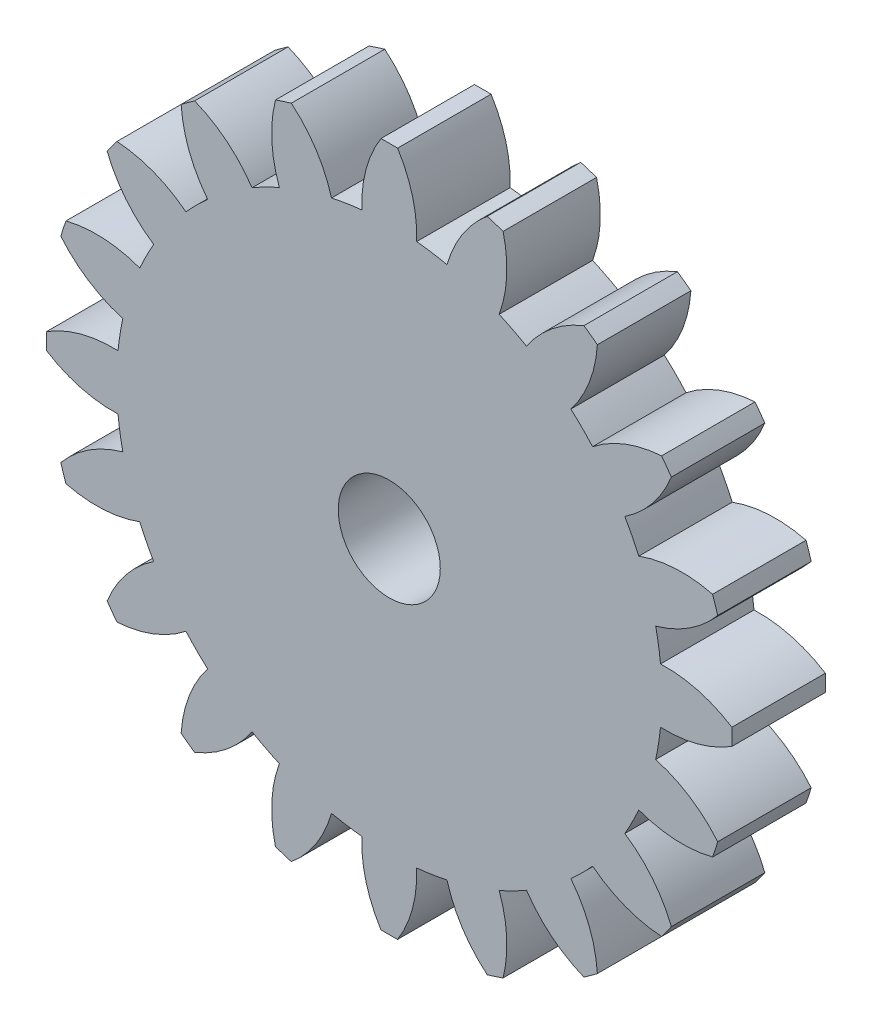
SolidWorks part; units mm, degrees
ref_plane "Front Plane" through (0, 0, 0) normal (0, 0, 1) x (1, 0, 0)
ref_plane "Top Plane" through (0, 0, 0) normal (0, 1, 0) x (1, 0, 0)
ref_plane "Right Plane" through (0, 0, 0) normal (1, 0, 0) x (0, 0, -1)
sketch "Sketch1" plane through (0, 0, 0) normal (0, 0, 1) x (1, 0, 0)
  point P0 (0, 22)
  arc B0 (12.4951, 18.1072) -> (8.8104, 15.1192) centre (15.4651, 10.679) ccw
  arc B1 (8.8104, 15.1192) -> (7.0531, 16.0147) centre (0, 0) ccw
  arc B2 (7.0531, 16.0147) -> (7.3046, 20.7519) centre (-0.4507, 18.7884) ccw
  arc B3 (7.3046, 20.7519) -> (6.2881, 21.0822) centre (0, 0) ccw
  arc B4 (6.2881, 21.0822) -> (3.7071, 17.1018) centre (11.4082, 14.9353) ccw
  arc B5 (3.7071, 17.1018) -> (1.7591, 17.4104) centre (0, 0) ccw
  arc B6 (1.7591, 17.4104) -> (0.5344, 21.9935) centre (-6.2346, 17.7296) ccw
  arc B7 (0.5344, 21.9935) -> (-0.5344, 21.9935) centre (0, 0) ccw
  arc B8 (-0.5344, 21.9935) -> (-1.7591, 17.4104) centre (6.2346, 17.7296) ccw
  arc B9 (-1.7591, 17.4104) -> (-3.7071, 17.1018) centre (0, 0) ccw
  arc B10 (-3.7071, 17.1018) -> (-6.2881, 21.0822) centre (-11.4082, 14.9353) ccw
  arc B11 (-6.2881, 21.0822) -> (-7.3046, 20.7519) centre (0, 0) ccw
  arc B12 (-7.3046, 20.7519) -> (-7.0531, 16.0147) centre (0.4507, 18.7884) ccw
  arc B13 (-7.0531, 16.0147) -> (-8.8104, 15.1192) centre (0, 0) ccw
  arc B14 (-8.8104, 15.1192) -> (-12.4951, 18.1072) centre (-15.4651, 10.679) ccw
  arc B15 (-12.4951, 18.1072) -> (-13.3598, 17.479) centre (0, 0) ccw
  arc B16 (-13.3598, 17.479) -> (-11.6567, 13.0513) centre (-5.3773, 18.0081) ccw
  arc B17 (-11.6567, 13.0513) -> (-13.0513, 11.6567) centre (0, 0) ccw
  arc B18 (-13.0513, 11.6567) -> (-17.479, 13.3598) centre (-18.0081, 5.3773) ccw
  arc B19 (-17.479, 13.3598) -> (-18.1072, 12.4951) centre (0, 0) ccw
  arc B20 (-18.1072, 12.4951) -> (-15.1192, 8.8104) centre (-10.679, 15.4651) ccw
  arc B21 (-15.1192, 8.8104) -> (-16.0147, 7.0531) centre (0, 0) ccw
  arc B22 (-16.0147, 7.0531) -> (-20.7519, 7.3046) centre (-18.7884, -0.4507) ccw
  arc B23 (-20.7519, 7.3046) -> (-21.0822, 6.2881) centre (0, 0) ccw
  arc B24 (-21.0822, 6.2881) -> (-17.1018, 3.7071) centre (-14.9353, 11.4082) ccw
  arc B25 (-17.1018, 3.7071) -> (-17.4104, 1.7591) centre (0, 0) ccw
  arc B26 (-17.4104, 1.7591) -> (-21.9935, 0.5344) centre (-17.7296, -6.2346) ccw
  arc B27 (-21.9935, 0.5344) -> (-21.9935, -0.5344) centre (0, 0) ccw
  arc B28 (-21.9935, -0.5344) -> (-17.4104, -1.7591) centre (-17.7296, 6.2346) ccw
  arc B29 (-17.4104, -1.7591) -> (-17.1018, -3.7071) centre (0, 0) ccw
  arc B30 (-17.1018, -3.7071) -> (-21.0822, -6.2881) centre (-14.9353, -11.4082) ccw
  arc B31 (-21.0822, -6.2881) -> (-20.7519, -7.3046) centre (0, 0) ccw
  arc B32 (-20.7519, -7.3046) -> (-16.0147, -7.0531) centre (-18.7884, 0.4507) ccw
  arc B33 (-16.0147, -7.0531) -> (-15.1192, -8.8104) centre (0, 0) ccw
  arc B34 (-15.1192, -8.8104) -> (-18.1072, -12.4951) centre (-10.679, -15.4651) ccw
  arc B35 (-18.1072, -12.4951) -> (-17.479, -13.3598) centre (0, 0) ccw
  arc B36 (-17.479, -13.3598) -> (-13.0513, -11.6567) centre (-18.0081, -5.3773) ccw
  arc B37 (-13.0513, -11.6567) -> (-11.6567, -13.0513) centre (0, 0) ccw
  arc B38 (-11.6567, -13.0513) -> (-13.3598, -17.479) centre (-5.3773, -18.0081) ccw
  arc B39 (-13.3598, -17.479) -> (-12.4951, -18.1072) centre (0, 0) ccw
  arc B40 (-12.4951, -18.1072) -> (-8.8104, -15.1192) centre (-15.4651, -10.679) ccw
  arc B41 (-8.8104, -15.1192) -> (-7.0531, -16.0147) centre (0, 0) ccw
  arc B42 (-7.0531, -16.0147) -> (-7.3046, -20.7519) centre (0.4507, -18.7884) ccw
  arc B43 (-7.3046, -20.7519) -> (-6.2881, -21.0822) centre (0, 0) ccw
  arc B44 (-6.2881, -21.0822) -> (-3.7071, -17.1018) centre (-11.4082, -14.9353) ccw
  arc B45 (-3.7071, -17.1018) -> (-1.7591, -17.4104) centre (0, 0) ccw
  arc B46 (-1.7591, -17.4104) -> (-0.5344, -21.9935) centre (6.2346, -17.7296) ccw
  arc B47 (-0.5344, -21.9935) -> (0.5344, -21.9935) centre (0, 0) ccw
  arc B48 (0.5344, -21.9935) -> (1.7591, -17.4104) centre (-6.2346, -17.7296) ccw
  arc B49 (1.7591, -17.4104) -> (3.7071, -17.1018) centre (0, 0) ccw
  arc B50 (3.7071, -17.1018) -> (6.2881, -21.0822) centre (11.4082, -14.9353) ccw
  arc B51 (6.2881, -21.0822) -> (7.3046, -20.7519) centre (0, 0) ccw
  arc B52 (7.3046, -20.7519) -> (7.0531, -16.0147) centre (-0.4507, -18.7884) ccw
  arc B53 (7.0531, -16.0147) -> (8.8104, -15.1192) centre (0, 0) ccw
  arc B54 (8.8104, -15.1192) -> (12.4951, -18.1072) centre (15.4651, -10.679) ccw
  arc B55 (12.4951, -18.1072) -> (13.3598, -17.479) centre (0, 0) ccw
  arc B56 (13.3598, -17.479) -> (11.6567, -13.0513) centre (5.3773, -18.0081) ccw
  arc B57 (11.6567, -13.0513) -> (13.0513, -11.6567) centre (0, 0) ccw
  arc B58 (13.0513, -11.6567) -> (17.479, -13.3598) centre (18.0081, -5.3773) ccw
  arc B59 (17.479, -13.3598) -> (18.1072, -12.4951) centre (0, 0) ccw
  arc B60 (18.1072, -12.4951) -> (15.1192, -8.8104) centre (10.679, -15.4651) ccw
  arc B61 (15.1192, -8.8104) -> (16.0147, -7.0531) centre (0, 0) ccw
  arc B62 (16.0147, -7.0531) -> (20.7519, -7.3046) centre (18.7884, 0.4507) ccw
  arc B63 (20.7519, -7.3046) -> (21.0822, -6.2881) centre (0, 0) ccw
  arc B64 (21.0822, -6.2881) -> (17.1018, -3.7071) centre (14.9353, -11.4082) ccw
  arc B65 (17.1018, -3.7071) -> (17.4104, -1.7591) centre (0, 0) ccw
  arc B66 (17.4104, -1.7591) -> (21.9935, -0.5344) centre (17.7296, 6.2346) ccw
  arc B67 (21.9935, -0.5344) -> (21.9935, 0.5344) centre (0, 0) ccw
  arc B68 (21.9935, 0.5344) -> (17.4104, 1.7591) centre (17.7296, -6.2346) ccw
  arc B69 (17.4104, 1.7591) -> (17.1018, 3.7071) centre (0, 0) ccw
  arc B70 (17.1018, 3.7071) -> (21.0822, 6.2881) centre (14.9353, 11.4082) ccw
  arc B71 (21.0822, 6.2881) -> (20.7519, 7.3046) centre (0, 0) ccw
  arc B72 (20.7519, 7.3046) -> (16.0147, 7.0531) centre (18.7884, -0.4507) ccw
  arc B73 (16.0147, 7.0531) -> (15.1192, 8.8104) centre (0, 0) ccw
  arc B74 (15.1192, 8.8104) -> (18.1072, 12.4951) centre (10.679, 15.4651) ccw
  arc B75 (18.1072, 12.4951) -> (17.479, 13.3598) centre (0, 0) ccw
  arc B76 (17.479, 13.3598) -> (13.0513, 11.6567) centre (18.0081, 5.3773) ccw
  arc B77 (13.0513, 11.6567) -> (11.6567, 13.0513) centre (0, 0) ccw
  arc B78 (11.6567, 13.0513) -> (13.3598, 17.479) centre (5.3773, 18.0081) ccw
  arc B79 (13.3598, 17.479) -> (12.4951, 18.1072) centre (0, 0) ccw
  circle B80 centre (0, 0) radius 2
sketch_block_instance "Block1-1"
sketch_block "Block1"
extrude "Boss-Extrude1" add sketch "Sketch1" along normal blind 6
sketch "Sketch2" plane through (0, 0, 6) normal (0, 0, 1) x (1, 0, 0)
  circle A0 centre (0, 0) radius 5.1392
extrude "Boss-Extrude2" add sketch "Sketch2" against normal up to surface (6 mm away) up to face at (0, 0, 0)
sketch "Sketch3" plane through (0, 0, 6) normal (0, 0, 1) x (1, 0, 0)
  circle A0 centre (0, 0) radius 3.275
  dimension "D1" = 6.55
extrude "Cut-Extrude1" cut sketch "Sketch3" against normal blind 10
